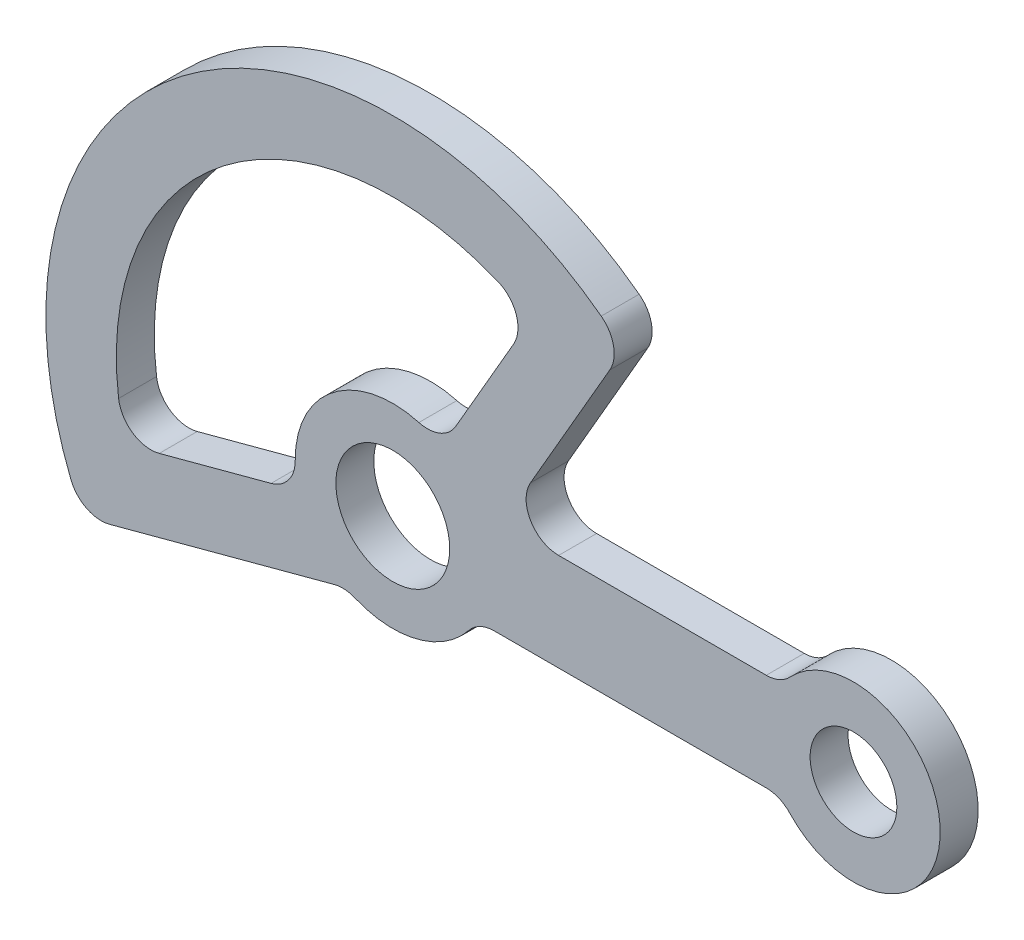
SolidWorks part; units mm, degrees
ref_plane "Front Plane" through (0, 0, 0) normal (0, 0, 1) x (1, 0, 0)
ref_plane "Top Plane" through (0, 0, 0) normal (0, 1, 0) x (1, 0, 0)
ref_plane "Right Plane" through (0, 0, 0) normal (1, 0, 0) x (0, 0, -1)
sketch "Sketch1" plane through (0, 0, 0) normal (0, 0, 1) x (1, 0, 0)
  line L0 (0, 0) -> (10.5, 0) construction
  line L1 (71.7712, 9) -> (20.2073, 9)
  line L2 (71.7712, -9) -> (15.5885, -9)
  line L3 (9, 15.5885) -> (25.5, 44.1673)
  line L4 (42.5912, 47.7702) -> (20.2073, 9)
  line L5 (0, 0) -> (0, 76.8198) construction
  line L7 (-57.1658, -28.7761) -> (-8.661, -15.7793)
  line L8 (-17.3867, -4.6587) -> (-49.2622, -13.1998)
  line L9 (77, 0) -> (183.4538, 0) construction
  circle A0 centre (0, 0) radius 10.5
  circle A1 centre (85, 0) radius 8
  arc A2 (71.7712, -9) -> (71.7712, 9) centre (85, 0) ccw
  arc A3 (9, 15.5885) -> (-17.3867, -4.6587) centre (0, 0) ccw
  arc A5 (42.5912, 47.7702) -> (-57.1658, -28.7761) centre (0, 0) ccw
  arc A6 (-8.661, -15.7793) -> (15.5885, -9) centre (0, 0) ccw
  arc A7 (25.5, 44.1673) -> (-49.2622, -13.1998) centre (0, 0) ccw
  point P22 (0, 0)
  point P23 (-1.3032, -10.4188)
  point P24 (0, 0)
  point P25 (9, -10.5)
  point P26 (0, 0)
  point P27 (12.7476, -2.5491)
  dimension "D1" = 32
  dimension "D2" = 16
  dimension "D4" = 128
  dimension "D6" = 36
  dimension "D7" = 21
  dimension "D3" = 18
  dimension "D8" = 85
  dimension "D9" = 13
  dimension "D10" = 30
extrude "Boss-Extrude2" add sketch "Sketch1" along normal blind 7
fillet "Fillet4" radius 6 7 edges at (71.7712, -9, 3.5) (15.5885, -9, 3.5) (-8.661, -15.7793, 3.5) (-57.1658, -28.7761, 3.5) (71.7712, 9, 3.5) (42.5912, 47.7702, 3.5) (20.2073, 9, 3.5)
fillet "Fillet5" radius 6 4 edges at (9, 15.5885, 3.5) (25.5, 44.1673, 3.5) (-17.3867, -4.6587, 3.5) (-49.2622, -13.1998, 3.5)
